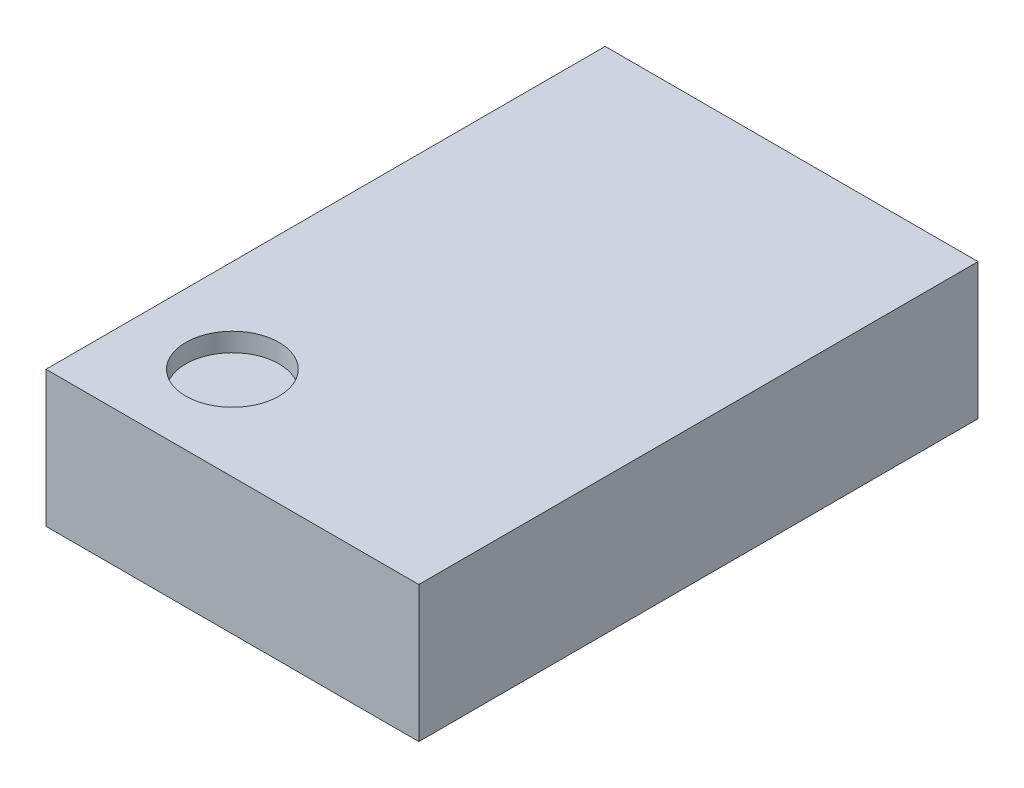
SolidWorks part; units mm, degrees
ref_plane "Front Plane" through (0, 0, 0) normal (0, 0, 1) x (1, 0, 0)
ref_plane "Top Plane" through (0, 0, 0) normal (0, 1, 0) x (1, 0, 0)
ref_plane "Right Plane" through (0, 0, 0) normal (1, 0, 0) x (0, 0, -1)
sketch "Sketch1" plane through (0, 0, 0) normal (0, 1, 0) x (1, 0, 0)
  line L1 (-1, 1.5) -> (1, 1.5)
  line L2 (-1, 1.5) -> (-1, -1.5)
  line L3 (-1, -1.5) -> (1, -1.5)
  line L4 (1, 1.5) -> (1, -1.5)
  line L5 (-1, 1.5) -> (1, -1.5) construction
  line L6 (-1, -1.5) -> (1, 1.5) construction
  point P0 (0, 0)
  dimension "D1" = 2
  dimension "D2" = 3
extrude "Boss-Extrude1" add sketch "Sketch1" along normal blind 0.73
sketch "Sketch2" plane through (0, 0.73, 0) normal (0, 1, 0) x (1, 0, 0)
  line L0 (-1, -1.5) -> (1, -1.5) construction
  line L1 (-1, 1.5) -> (-1, -1.5) construction
  circle A0 centre (-0.5, -1) radius 0.25
  dimension "D3" = 0.5
  dimension "D1" = 0.5
  dimension "D2" = 0.5
extrude "Cut-Extrude1" cut sketch "Sketch2" against normal blind 0.1
